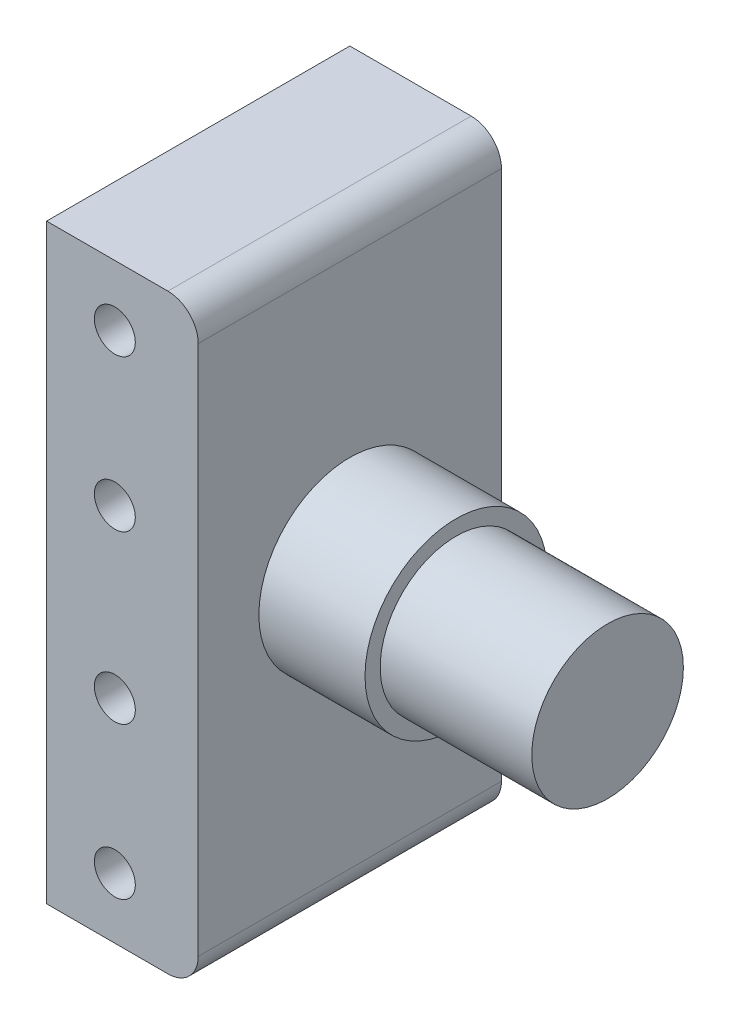
SolidWorks part; units mm, degrees
ref_plane "Front Plane" through (0, 0, 0) normal (0, 0, 1) x (1, 0, 0)
ref_plane "Top Plane" through (0, 0, 0) normal (0, 1, 0) x (1, 0, 0)
ref_plane "Right Plane" through (0, 0, 0) normal (1, 0, 0) x (0, 0, -1)
sketch "Sketch1" plane through (0, 0, 0) normal (0, 0, 1) x (1, 0, 0)
  line L1 (-5, -19.5) -> (3, -19.5)
  line L2 (-5, -19.5) -> (-5, 19.5)
  line L3 (-5, 19.5) -> (3, 19.5)
  line L4 (5, -17.5) -> (5, 17.5)
  line L5 (-5, -19.5) -> (5, 19.5) construction
  line L6 (-5, 19.5) -> (5, -19.5) construction
  arc A0 (3, -19.5) -> (5, -17.5) centre (3, -17.5) ccw
  arc A1 (3, 19.5) -> (5, 17.5) centre (3, 17.5) cw
  point P0 (0, 0)
  dimension "D3" = 2
  dimension "D1" = 39
  dimension "D2" = 10
extrude "Boss-Extrude1" add sketch "Sketch1" along normal blind 20
sketch "Sketch2" plane through (0, 0, 20) normal (0, 0, 1) x (1, 0, 0)
  line L3 (-5, 19.5) -> (-5, -19.5) construction
  line L4 (-5, 0) -> (5, 0) construction
  line L5 (5, -17.5) -> (5, 17.5) construction
  line L6 (-0.5, 5.5) -> (-0.5, -5.5) construction
  circle A0 centre (-0.5, 15.5) radius 1.35
  circle A4 centre (-0.5, 5.5) radius 1.35
  circle A5 centre (-0.5, -15.5) radius 1.35
  circle A6 centre (-0.5, -5.5) radius 1.35
  dimension "D1" = 11
  dimension "D2" = 4.5
  dimension "D3" = 2.7
  dimension "D5" = 10
  dimension "D4" = 2
extrude "Cut-Extrude2" cut sketch "Sketch2" against normal blind 12
sketch "Sketch3" plane through (5, 0, 0) normal (1, 0, 0) x (0, 0, -1)
  line L0 (-20, -17.5) -> (0, 17.5) construction
  circle A0 centre (-10, 0) radius 5
  dimension "D1" = 10
extrude "Boss-Extrude2" add sketch "Sketch3" along normal blind 17
sketch "Sketch4" plane through (5, 0, 0) normal (1, 0, 0) x (0, 0, -1)
  circle A0 centre (-10, 0) radius 6
  dimension "D1" = 12
extrude "Boss-Extrude3" add sketch "Sketch4" along normal blind 7
